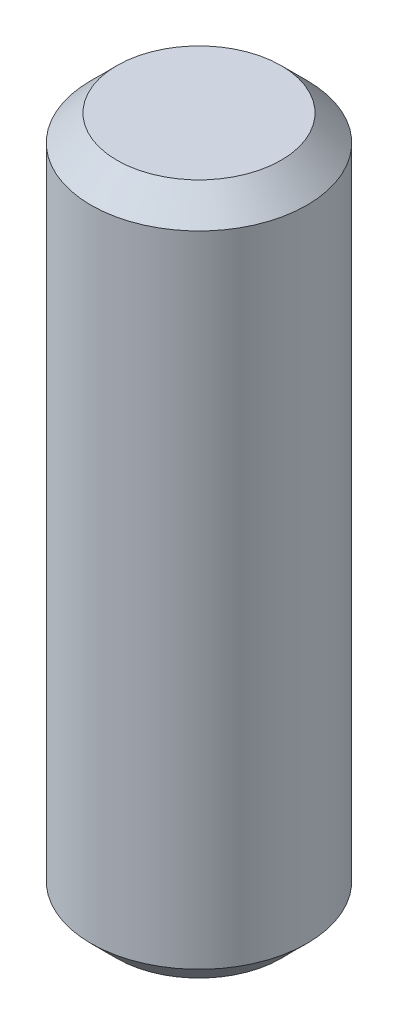
SolidWorks part; units mm, degrees
ref_plane "Front Plane" through (0, 0, 0) normal (0, 0, 1) x (1, 0, 0)
ref_plane "Top Plane" through (0, 0, 0) normal (0, 1, 0) x (1, 0, 0)
ref_plane "Right Plane" through (0, 0, 0) normal (1, 0, 0) x (0, 0, -1)
sketch "Sketch2" plane through (0, 0, 0) normal (0, 1, 0) x (1, 0, 0)
  circle A0 centre (0, 0) radius 6.35
  dimension "D1" = 12.7
extrude "Boss-Extrude1" add sketch "Sketch2" along normal blind 40.64
chamfer "Chamfer1" distance 1.524 angle 45 2 edges at (0, 0, 6.35) (0, 40.64, 6.35)
